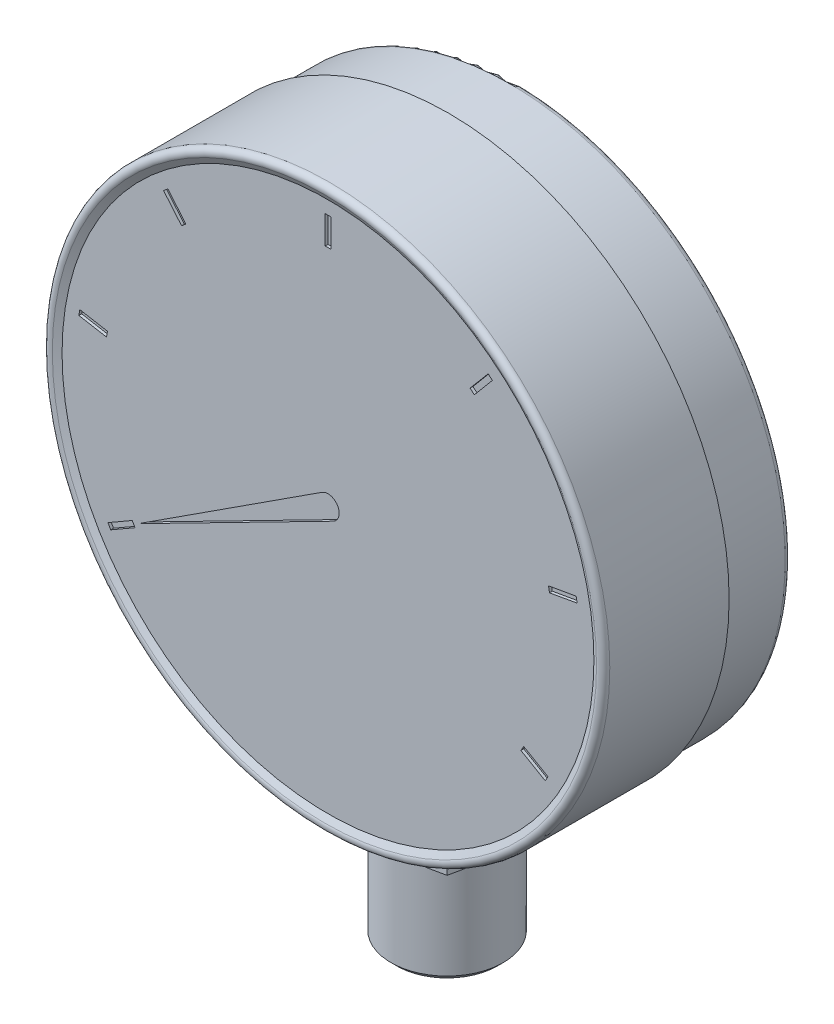
SolidWorks part; units mm, degrees
ref_plane "Horní" through (0, 0, 0) normal (0, 0, 1) x (1, 0, 0)
ref_plane "Přední" through (0, 0, 0) normal (0, 1, 0) x (1, 0, 0)
ref_plane "Pravá" through (0, 0, 0) normal (1, 0, 0) x (0, 0, -1)
sketch "Skica1" plane through (0, 0, 0) normal (1, 0, 0) x (0, 0, -1)
  line L0 (0, 50) -> (1.5, 47.4019)
  line L1 (0, 50) -> (23, 50)
  line L4 (35, 49) -> (35, 0)
  line L7 (35, 0) -> (1.5, 0)
  line L8 (0, 0) -> (-34.5616, 0) construction
  line L10 (1.5, 47.4019) -> (1.5, 0)
  line L12 (23, 50) -> (23, 49)
  line L13 (23, 49) -> (35, 49)
  dimension "D2" = 100
  dimension "D4" = 98
  dimension "D7" = 30
  dimension "D8" = 1.5
  dimension "D9" = 35
  dimension "D12" = 23
revolve "Rotovat1" add sketch "Skica1" angle 360 about L8
fillet "Zaoblit1" radius 1 2 edges at (-50, 0, 0) (-49, 0, -35)
sketch "Skica2" plane through (0, 0, -1.5) normal (0, 0, 1) x (1, 0, 0)
  line L0 (0, 45) -> (0, 0) construction
  line L3 (0.5, 40) -> (0.5, 45)
  line L4 (0.5, 40) -> (-0.5, 40)
  line L5 (0.5, 45) -> (-0.5, 45)
  line L6 (-0.5, 40) -> (-0.5, 45)
  dimension "D1" = 45
  dimension "D2" = 1
  dimension "D3" = 5
extrude "Odebrat vysunutím1" cut sketch "Skica2" against normal blind 0.5
pattern_circular "Kruhové pole1" count 9 over 360 about axis through (0, 0, 0) along (0, 0, 1) skipping 4, 5 of "Odebrat vysunutím1"
sketch "Skica3" plane through (0, 0, -1.5) normal (0, 0, 1) x (1, 0, 0)
  line L0 (-1.0875, 1.6785) -> (-33.775, -19.5)
  line L1 (-33.775, -19.5) -> (0.9099, -1.7811)
  line L2 (0, 0) -> (-33.775, -19.5) construction
  line L3 (-38.7211, -22.933) -> (-34.391, -20.433) construction
  arc A0 (0.9099, -1.7811) -> (-1.0875, 1.6785) centre (0, 0) ccw
  dimension "D1" = 2
  dimension "D2" = 39
extrude "Odebrat vysunutím2" cut sketch "Skica3" against normal blind 0.5
sketch "Skica4" plane through (0, 0, 0) normal (0, 1, 0) x (1, 0, 0)
  line L0 (-49, 0.7321) -> (49, 0.7321) construction
  line L1 (-11, 33.7321) -> (11, 33.7321)
  line L2 (-11, 33.7321) -> (-11, 11.7321)
  line L3 (-11, 11.7321) -> (11, 11.7321)
  line L4 (11, 33.7321) -> (11, 11.7321)
  line L5 (0, 33.7321) -> (0, 11.7321) construction
  dimension "D1" = 11
  dimension "D2" = 22
extrude "Přidat vysunutím1" add sketch "Skica4" against normal blind 80
sketch "Skica5" plane through (0, 0, 0) normal (1, 0, 0) x (0, 0, -1)
  line L0 (22.7321, -80) -> (22.7321, -54.3084) construction
  line L1 (11.7321, -80) -> (33.7321, -80) construction
  line L3 (-8.2679, -52.3731) -> (12.7321, -58)
  line L5 (12.7321, -58) -> (12.7321, -77)
  line L6 (12.7321, -77) -> (19.7321, -77)
  line L7 (19.7321, -77) -> (19.7321, -80)
  line L8 (-8.2679, -80) -> (19.7321, -80)
  line L9 (-8.2679, -80) -> (-8.2679, -52.3731)
  line L10 (11.7321, -80) -> (11.7321, -48.775) construction
  line L11 (11.7321, -80) -> (11.7321, -48.775) construction
  dimension "D1" = 22
  dimension "D2" = 6
  dimension "D3" = 3
  dimension "D4" = 20
  dimension "D5" = 20
  dimension "D6" = 15
revolve "Odebrat rotací1" cut sketch "Skica5" angle 360 about L0
chamfer "Zkosení1" distance 1 angle 45 1 edges at (0, -77, -32.7321)
